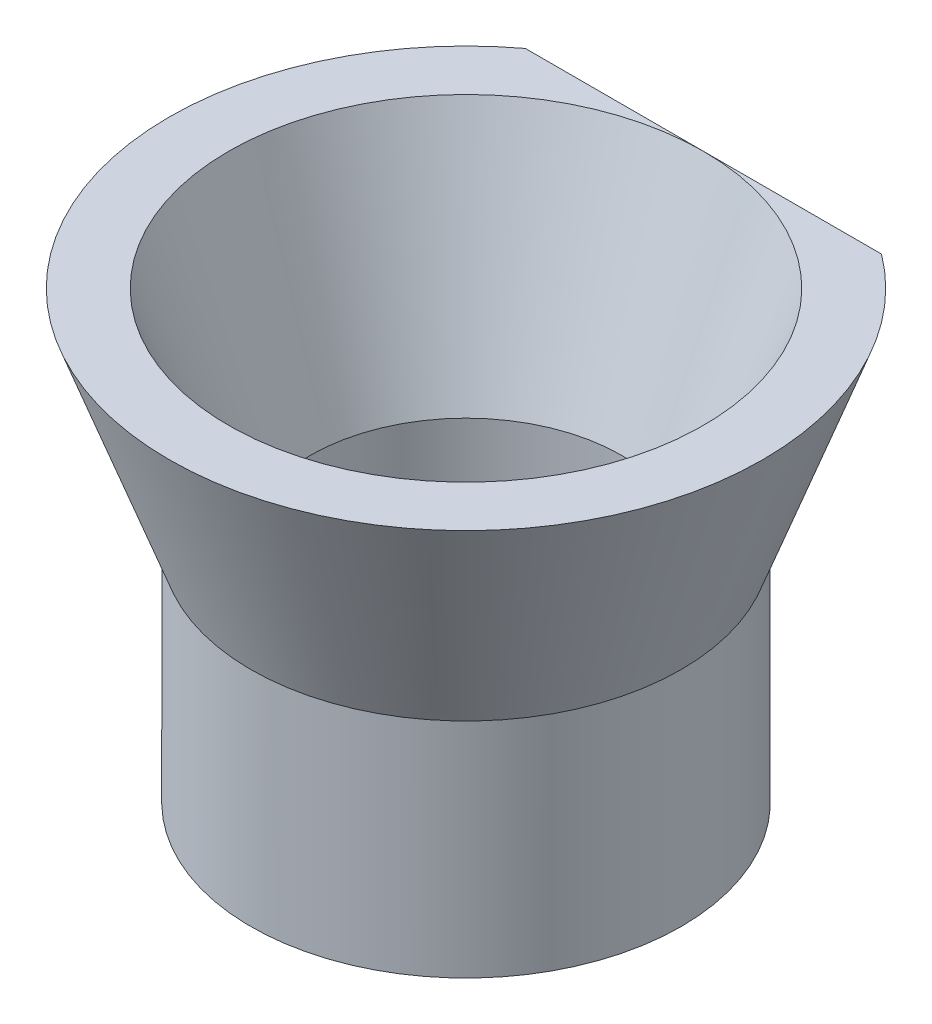
SolidWorks part; units mm, degrees
ref_plane "Alzado" through (0, 0, 0) normal (0, 0, 1) x (1, 0, 0)
ref_plane "Planta" through (0, 0, 0) normal (0, 1, 0) x (1, 0, 0)
ref_plane "Vista lateral" through (0, 0, 0) normal (1, 0, 0) x (0, 0, -1)
sketch "Croquis1" plane through (0, 0, 0) normal (0, 0, 1) x (1, 0, 0)
  line L0 (0, 7.5) -> (0, 0) construction
  line L1 (0, 0) -> (-5.25, 0) construction
  line L2 (-5.25, 0) -> (-8, 7.5)
  line L3 (-8, 7.5) -> (0, 7.5) construction
  line L4 (-8, 7.5) -> (-10, 7.5)
  line L5 (-10, 7.5) -> (-7.25, 0)
  line L6 (-7.25, 0) -> (-5.25, 0)
  dimension "D1" = 8
  dimension "D2" = 5.25
  dimension "D3" = 7.5
  dimension "D4" = 2
  dimension "D5" = 2
revolve "Revolución1" add sketch "Croquis1" angle 360 about L0
sketch "Croquis2" plane through (0, 0, 0) normal (0, -1, 0) x (1, 0, 0)
  circle A0 centre (0, 0) radius 5.25
  circle A1 centre (0, 0) radius 7.25
  dimension "D1" = 2
  dimension "D2" = 10.5
extrude "Saliente-Extruir1" add sketch "Croquis2" along normal blind 7.5
sketch "Croquis4" plane through (0, 7.5, 0) normal (0, 1, 0) x (1, 0, 0)
  line L0 (-8.6041, 8) -> (8.6041, 8)
  line L1 (8.6041, 8) -> (0, 12.592)
  line L2 (0, 12.592) -> (-8.6041, 8)
  point P3 (0, 8)
extrude "Cortar-Extruir1" cut sketch "Croquis4" against normal blind 7.5
